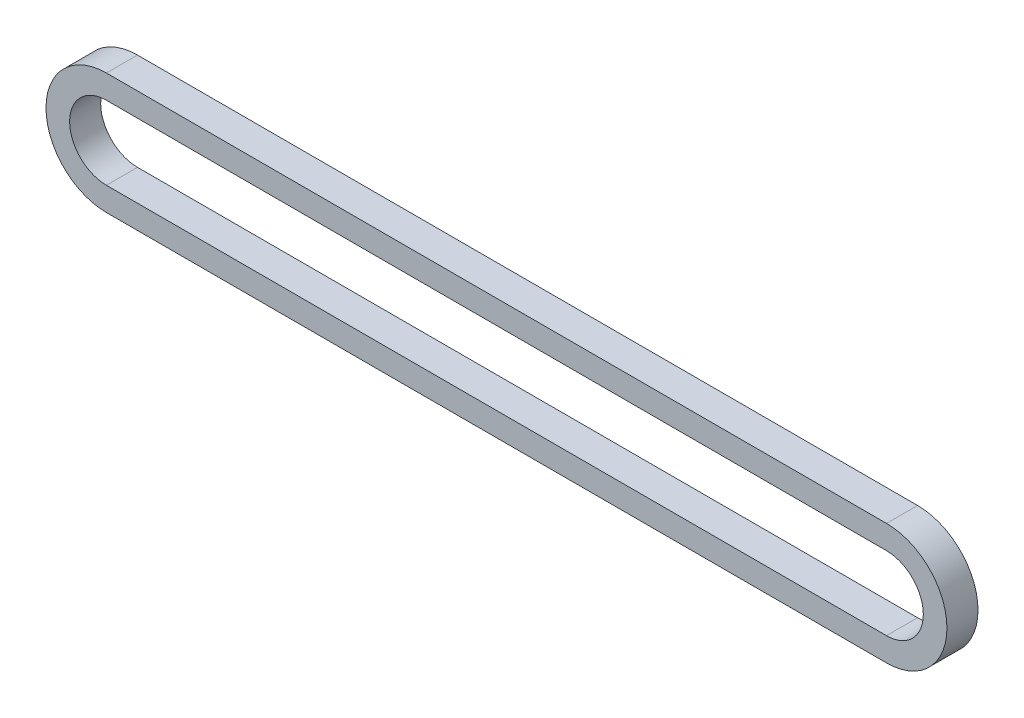
SolidWorks part; units mm, degrees
ref_plane "Front Plane" through (0, 0, 0) normal (0, 0, 1) x (1, 0, 0)
ref_plane "Top Plane" through (0, 0, 0) normal (0, 1, 0) x (1, 0, 0)
ref_plane "Right Plane" through (0, 0, 0) normal (1, 0, 0) x (0, 0, -1)
sketch "Sketch1" plane through (0, 0, 0) normal (0, 0, 1) x (1, 0, 0)
  line L0 (0, 18.4009) -> (295.275, 18.4009)
  line L1 (0, -18.4009) -> (295.275, -18.4009)
  line L2 (0, 0) -> (295.275, 0) construction
  arc A0 (0, 18.4009) -> (0, -18.4009) centre (0, 0) ccw
  arc A1 (295.275, -18.4009) -> (295.275, 18.4009) centre (295.275, 0) ccw
  dimension "D2" = 36.8018
  dimension "D3" = 36.8018
  dimension "D1" = 295.275
extrude "Extrude-Thin1" add sketch "Sketch1" along normal mid plane 11.7602 thin thin type mid plane wall 8.9408
equation "\"Center Distance\"= 11.625"
equation "\"D1@Sketch1\"=\"Center Distance\""
equation "\"Pitch\"= 0.375"
equation "\"T1\"= 12"
equation "\"T2\"= 12"
equation "\"D2@Sketch1\"=\"Pitch\"/(sin( 180/\"T1\"))"
equation "\"D3@Sketch1\"=\"Pitch\"/(sin( 180/\"T2\"))"
equation "\"Links\"= 2 * \"Center Distance\" / \"Pitch\" + ( \"T1\" + \"T2\" ) / 2 + ( ( \"T2\" - \"T1\" ) / ( 2 * 3.14159 ) ) ^ 2 * \"Pitch\" / \"Center Distance\""
